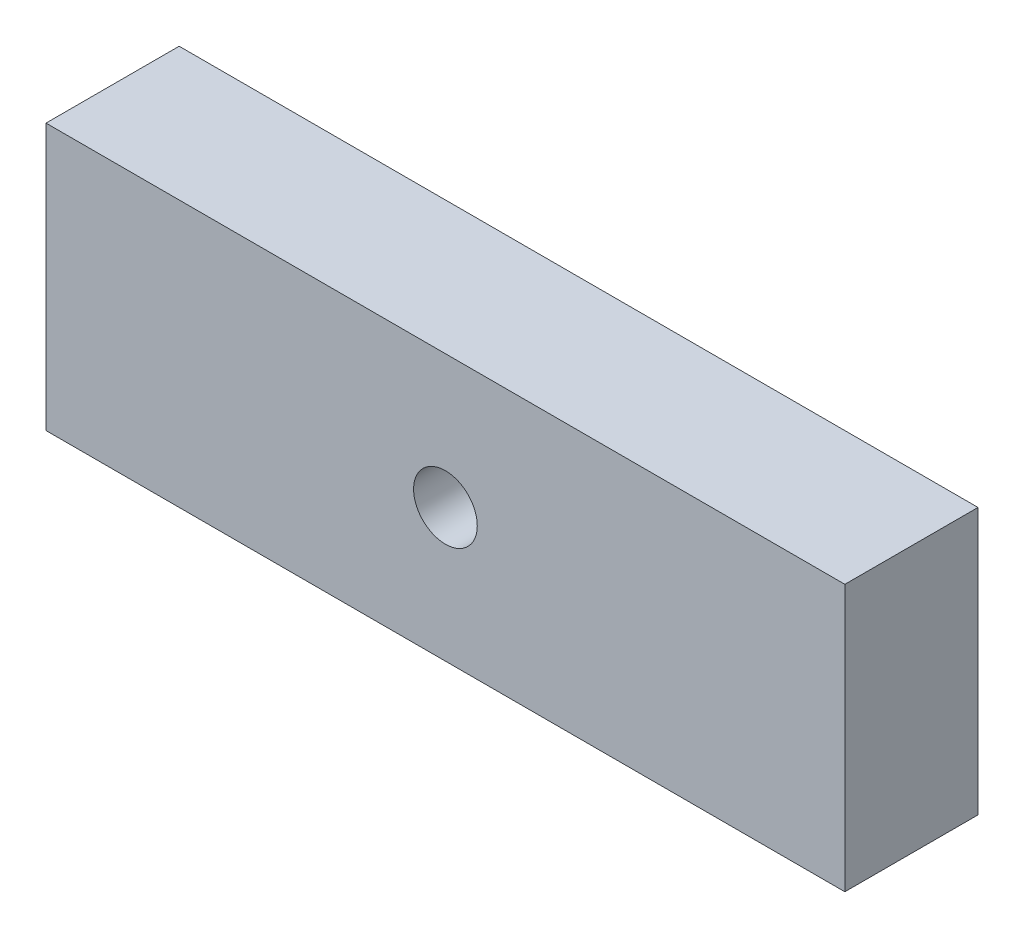
SolidWorks part; units mm, degrees
ref_plane "Front Plane" through (0, 0, 0) normal (0, 0, 1) x (1, 0, 0)
ref_plane "Top Plane" through (0, 0, 0) normal (0, 1, 0) x (1, 0, 0)
ref_plane "Right Plane" through (0, 0, 0) normal (1, 0, 0) x (0, 0, -1)
sketch "Sketch1" plane through (0, 0, 0) normal (0, 0, 1) x (1, 0, 0)
  line L1 (0, 0) -> (47.625, 0)
  line L2 (0, 0) -> (0, 15.875)
  line L3 (0, 15.875) -> (47.625, 15.875)
  line L4 (47.625, 0) -> (47.625, 15.875)
  dimension "D1" = 15.875
  dimension "D2" = 47.625
extrude "Boss-Extrude1" add sketch "Sketch1" along normal blind 7.9375
hole_wizard "#6 Clearance Hole1" positions "Sketch2" profile "Sketch3" hole size "#6" standard "ANSI Inch" end condition up to next
sketch "Sketch2" plane through (0, 0, 7.9375) normal (0, 0, 1) x (1, 0, 0)
  line L2 (23.8125, 15.875) -> (23.8125, 0) construction
  line L3 (47.625, 15.875) -> (0, 15.875) construction
  line L4 (0, 0) -> (47.625, 0) construction
  line L6 (0, 15.875) -> (0, 0) construction
  line L7 (0, 7.9375) -> (47.625, 7.9375) construction
  line L8 (47.625, 0) -> (47.625, 15.875) construction
  point P0 (23.8125, 7.9375)
sketch "Sketch3" plane through (23.8125, 7.9375, 7.9375) normal (1, 0, 0) x (0, -1, 0)
  line L0 (0, 0) -> (0, 7.9375)
  line L1 (0, 7.9375) -> (1.8986, 7.9375)
  line L2 (1.8986, 7.9375) -> (1.8986, 0)
  line L5 (1.8986, 0) -> (0, 0)
  line L11 (0, -6.35) -> (0, 107.95) construction
  dimension "Thru Hole Dia." = 3.7973
  dimension "Thru Hole Depth" = 7.9375
